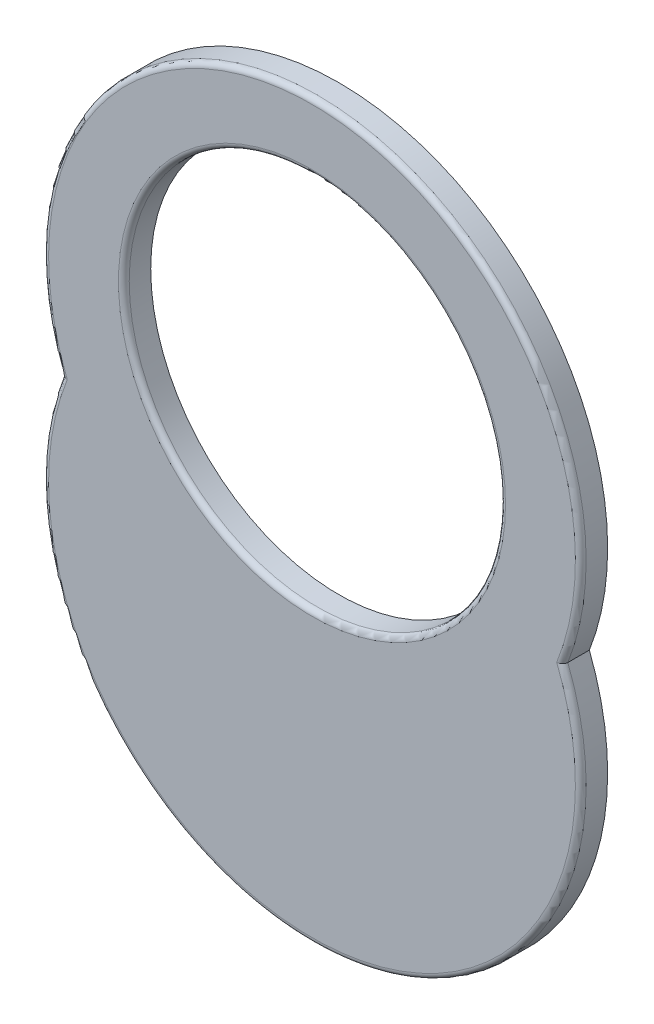
SolidWorks part; units mm, degrees
ref_plane "Front Plane" through (0, 0, 0) normal (0, 0, 1) x (1, 0, 0)
ref_plane "Top Plane" through (0, 0, 0) normal (0, 1, 0) x (1, 0, 0)
ref_plane "Right Plane" through (0, 0, 0) normal (1, 0, 0) x (0, 0, -1)
sketch "Szkic1" plane through (0, 0, 0) normal (0, 0, 1) x (1, 0, 0)
  arc A0 (-18.6397, 7.25) -> (18.6397, 7.25) centre (0, 0) ccw
  arc A1 (18.6397, 7.25) -> (-18.6397, 7.25) centre (0, 14.5) ccw
  circle A2 centre (0, 15.5) radius 14
  dimension "D1" = 40
  dimension "D3" = 28
  dimension "D2" = 14.5
  dimension "D4" = 1
extrude "Dodanie-wyciągnięcie1" add sketch "Szkic1" along normal blind 2
fillet "Zaokrąglenie1" radius 0.4 3 edges at (14, 15.5, 2) (0, -20, 2) (0, 34.5, 2)
